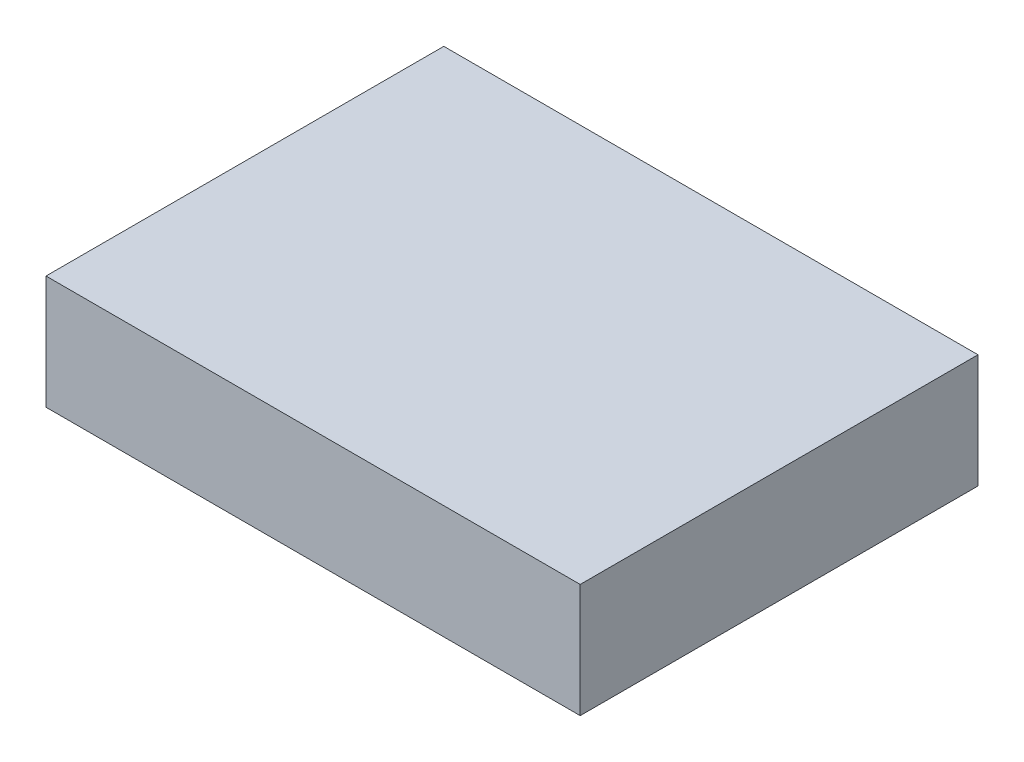
SolidWorks part; units mm, degrees
ref_plane "Front Plane" through (0, 0, 0) normal (0, 0, 1) x (1, 0, 0)
ref_plane "Top Plane" through (0, 0, 0) normal (0, 1, 0) x (1, 0, 0)
ref_plane "Right Plane" through (0, 0, 0) normal (1, 0, 0) x (0, 0, -1)
sketch "Sketch1" plane through (0, 0, 0) normal (0, 1, 0) x (1, 0, 0)
  line L0 (0, 0) -> (-23.5, 0) construction
  line L1 (-23.5, 17.5) -> (23.5, 17.5)
  line L2 (-23.5, 17.5) -> (-23.5, -17.5)
  line L3 (-23.5, -17.5) -> (23.5, -17.5)
  line L4 (23.5, 17.5) -> (23.5, -17.5)
  line L5 (0, 0) -> (0, -17.5) construction
  dimension "D1" = 47
  dimension "D2" = 35
extrude "Boss-Extrude1" add sketch "Sketch1" along normal blind 10
